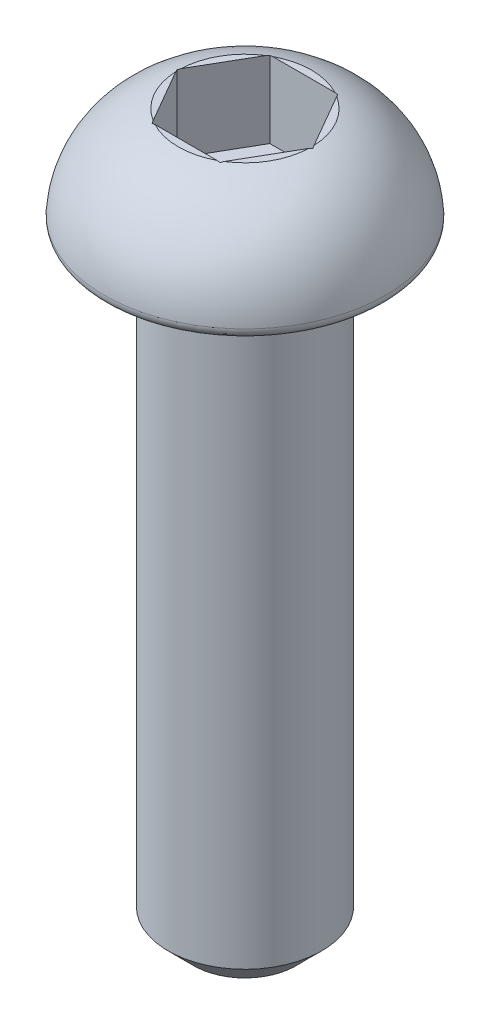
SolidWorks part; units mm, degrees
ref_plane "前视" through (0, 0, 0) normal (0, 0, 1) x (1, 0, 0)
ref_plane "上视" through (0, 0, 0) normal (0, 1, 0) x (1, 0, 0)
ref_plane "右视" through (0, 0, 0) normal (1, 0, 0) x (0, 0, -1)
sketch "草图1" plane through (0, 0, 0) normal (0, 0, 1) x (1, 0, 0)
  line L0 (0, 0) -> (0, 2)
  line L1 (0, 2) -> (1.3, 2)
  line L2 (0, 0) -> (2.75, 0)
  arc A0 (1.3, 2) -> (2.75, 0) centre (0.7515, 0.0767) cw
  dimension "D4" = 2
  dimension "D1" = 1.3
  dimension "D2" = 2.75
  dimension "D3" = 2
revolve "旋转1" add sketch "草图1" angle 360 about L0
fillet "圆角1" radius 0.2 1 edges at (0, 0, -2.75)
sketch "草图2" plane through (0, 2, 0) normal (0, 1, 0) x (1, 0, 0)
  line L1 (1.3279, 0) -> (0.664, 1.15)
  line L2 (0.664, 1.15) -> (-0.664, 1.15)
  line L3 (-0.664, 1.15) -> (-1.3279, 0)
  line L4 (-1.3279, 0) -> (-0.664, -1.15)
  line L5 (-0.664, -1.15) -> (0.664, -1.15)
  line L6 (0.664, -1.15) -> (1.3279, 0)
  circle A0 centre (0, 0) radius 1.15 construction
  dimension "D1" = 2.3
extrude "切除-拉伸1" cut sketch "草图2" against normal blind 1.5
sketch "草图3" plane through (0, 0, 0) normal (0, -1, 0) x (1, 0, 0)
  circle A0 centre (0, 0) radius 1.5
  dimension "D1" = 3
extrude "凸台-拉伸1" add sketch "草图3" along normal blind 12
chamfer "倒角1" distance 0.5 angle 45 1 edges at (0, -12, -1.5)
